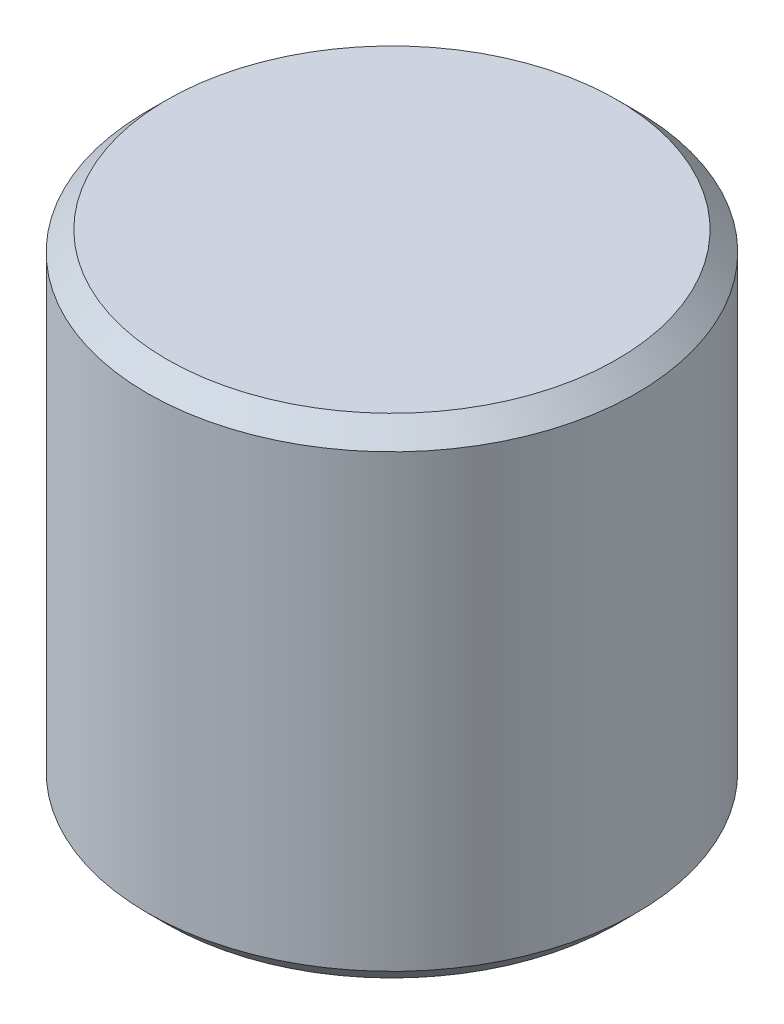
SolidWorks part; units mm, degrees
ref_plane "Front Plane" through (0, 0, 0) normal (0, 0, 1) x (1, 0, 0)
ref_plane "Top Plane" through (0, 0, 0) normal (0, 1, 0) x (1, 0, 0)
ref_plane "Right Plane" through (0, 0, 0) normal (1, 0, 0) x (0, 0, -1)
sketch "Sketch1" plane through (0, 0, 0) normal (0, 1, 0) x (1, 0, 0)
  circle A0 centre (0, 0) radius 5
  dimension "D1" = 10
extrude "Boss-Extrude1" add sketch "Sketch1" along normal blind 10
chamfer "Chamfer1" distance 0.4 angle 45 2 edges at (0, 0, 5) (0, 10, 5)
